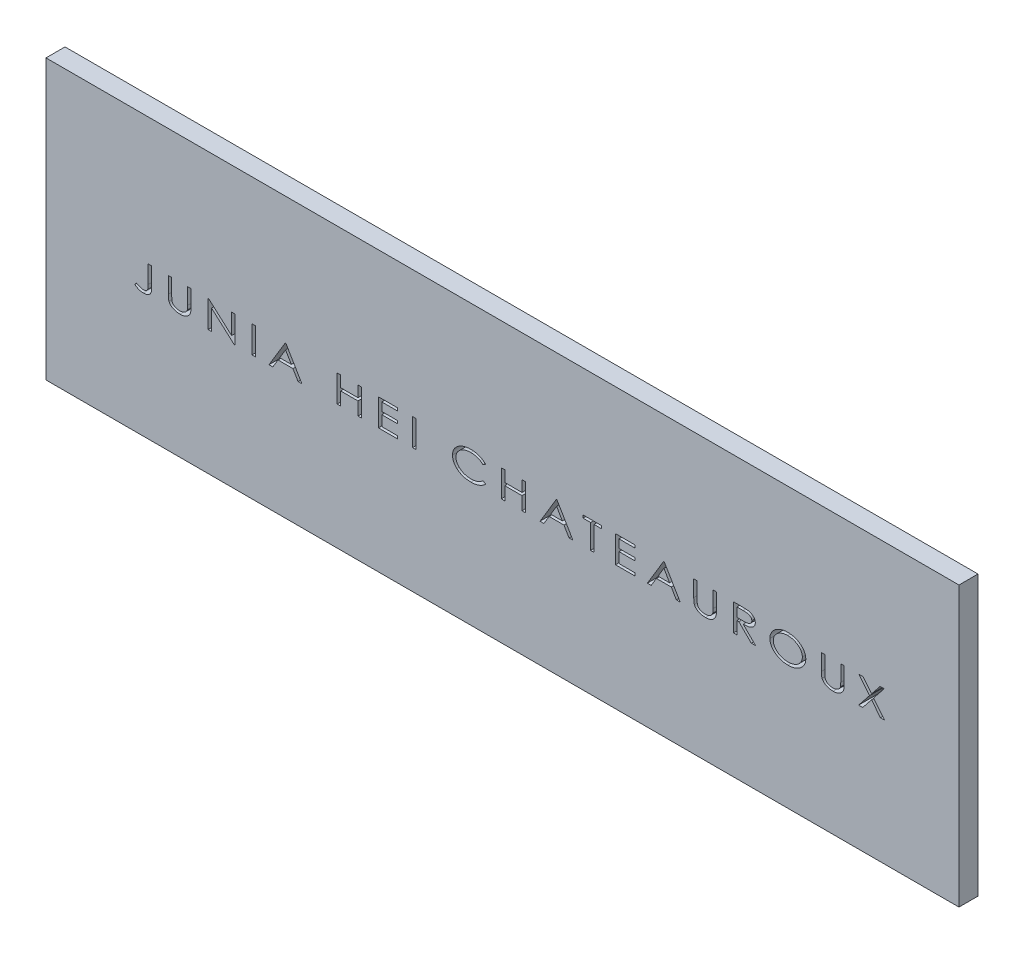
SolidWorks part; units mm, degrees
ref_plane "Front Plane" through (0, 0, 0) normal (0, 0, 1) x (1, 0, 0)
ref_plane "Top Plane" through (0, 0, 0) normal (0, 1, 0) x (1, 0, 0)
ref_plane "Right Plane" through (0, 0, 0) normal (1, 0, 0) x (0, 0, -1)
sketch "Sketch1" plane through (0, 0, 0) normal (0, 0, 1) x (1, 0, 0)
  line L3 (0, 288) -> (288, 288)
  line L9 (0, 200) -> (288, 200)
  line L10 (288, 200) -> (288, 288)
  line L11 (0, 200) -> (0, 288)
  dimension "D1" = 288
  dimension "D3" = 88
extrude "Boss-Extrude2" add sketch "Sketch1" along normal blind 6
sketch "Sketch4" plane through (0, 0, 0) normal (0, 0, -1) x (-1, 0, 0)
  text T0 "JUNIA HEI CHATEAUROUX" font "Century Gothic" height 8.5
extrude "Cut-Extrude1" cut sketch "Sketch4" against normal blind 6
